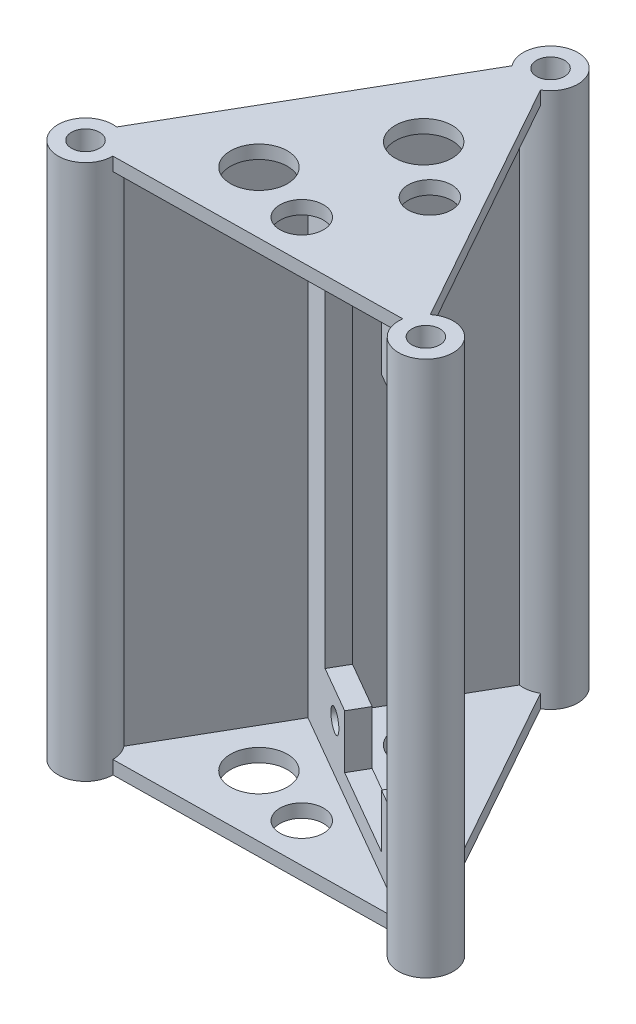
SolidWorks part; units mm, degrees
ref_plane "Front Plane" through (0, 0, 0) normal (0, 0, 1) x (1, 0, 0)
ref_plane "Top Plane" through (0, 0, 0) normal (0, 1, 0) x (1, 0, 0)
ref_plane "Right Plane" through (0, 0, 0) normal (1, 0, 0) x (0, 0, -1)
sketch "Sketch1" plane through (0, 0, 0) normal (0, 1, 0) x (1, 0, 0)
  line L0 (0, 0) -> (0, 38.1)
  circle A0 centre (0, 0) radius 38.1
  circle A1 centre (0, 29.337) radius 1.5875
  circle A2 centre (25.4066, -14.6685) radius 1.5875
  circle A3 centre (-25.4066, -14.6685) radius 1.5875
  point P13 (0, 0)
  dimension "D1" = 76.2
  dimension "D2" = 3.175
  dimension ".345" = 8.763
  dimension "D4" = 3
extrude "Boss-Extrude1" add sketch "Sketch1" along normal blind 10
sketch "Sketch2" plane through (0, 10, 0) normal (0, 1, 0) x (1, 0, 0)
  line L0 (-25.4066, -14.6685) -> (0, 29.337)
  line L1 (-12.7033, 7.3342) -> (25.4066, -14.6685)
  line L2 (-24.1075, -15.4185) -> (1.299, 28.587)
  line L3 (-13.4533, 6.0352) -> (24.6566, -15.9675)
  line L4 (-26.7056, -13.9185) -> (-1.299, 30.087)
  line L5 (-11.9533, 8.6333) -> (26.1566, -13.3695)
  circle A0 centre (-25.4066, -14.6685) radius 1.5875
  circle A1 centre (0, 29.337) radius 1.5875
  circle A2 centre (25.4066, -14.6685) radius 1.5875
  circle A3 centre (-25.4066, -14.6685) radius 2.0875
  circle A4 centre (25.4066, -14.6685) radius 2.0875
  circle A5 centre (0, 29.337) radius 2.0875
  circle A6 centre (-25.4066, -14.6685) radius 4.0875
  circle A7 centre (0, 29.337) radius 4.0875
  circle A8 centre (25.4066, -14.6685) radius 4.0875
  dimension "D1" = 1.5
  dimension "D2" = 1.5
  dimension "D3" = 0.5
  dimension "D4" = 2
extrude "Boss-Extrude2" add sketch "Sketch2" along normal blind 80 separate body contours A7 L4 A6 L0 | A6 L2 L3 L0 | L4 A6 L2 A3 | L0 A6 L4 A3 | L2 A6 L0 A3 | L2 A7 L4 A5 | L4 A7 L0 A5 | L0 A7 L2 A5 | A7 L0 L5 L2 | L0 L3 L2 L1 | L5 L0 L1 L2 | A8 L5 L2 L1 | A8 L1 L2 L3 | L5 A8 L1 A4 | L1 A8 L3 A4 | L3 A8 L5 A4
delete or keep bodies "Body-Delete/Keep 1" type delete bodies bodies 101
sketch "Sketch3" plane through (0, 90, 0) normal (0, 1, 0) x (1, 0, 0)
  line L0 (21.3637, -14.0664) -> (-21.3191, -14.6685)
  line L1 (-12.1543, 5.2852) -> (21.3637, -14.0664) construction
  arc A0 (-24.8045, -10.6256) -> (-22.2064, -12.1256) centre (-25.4066, -14.6685) ccw construction
rib "Rib1" sketch "Sketch3" sketch "Sketch3" thickness 2 extrusion direction parallel to sketch draft on no parameters "D1"=2
sketch "Sketch5" plane through (0, 88, 0) normal (0, -1, 0) x (1, 0, 0)
  line L0 (-22.2064, 12.1256) -> (-12.1543, -5.2852) construction
  line L1 (-12.1543, -5.2852) -> (21.3637, 14.0664) construction
  circle A0 centre (-8.9761, 5.21) radius 4.25
  circle A1 centre (0.6842, 8.4779) radius 3.25
  dimension "D2" = 8.5
  dimension "D6" = 6.5
  dimension "D1" = 8
  dimension "D3" = 7.5
  dimension "D4" = 5.5
  dimension "D5" = 18
extrude "Cut-Extrude1" cut sketch "Sketch5" against normal up to surface (2 mm away) contours A1 | A0 up to face at (25.4066, 90, 16.756)
ref_plane "Plane1" through (0, 0, 0) normal (0.5, 0, -0.866) x (-0.866, 0, -0.5)
ref_plane "Plane2" through (0, 50, 0) normal (0, 1, 0) x (1, 0, 0)
mirror "Mirror1" about plane through (0, 50, 0) normal (0, 1, 0) of "Cut-Extrude1", "Rib1"
mirror "Mirror2" about plane through (0, 0, 0) normal (0.5, 0, -0.866) of "Mirror1", "Rib1", "Cut-Extrude1"
ref_plane "Plane3" through (0, 50, 0) normal (0, -1, 0) x (-1, 0, 0)
ref_plane "Plane4" through (22.8637, 12, 11.4683) normal (0, -1, 0) x (-1, 0, 0)
sketch "Sketch11" plane through (0.75, 0, -1.299) normal (0.5, 0, -0.866) x (-0.866, 0, -0.5)
  line L0 (8.8169, 84.125) -> (13.1685, 84.125) construction
  line L1 (8.8169, 84.125) -> (-21.1831, 84.125)
  line L2 (8.8169, 84.125) -> (8.8169, 15.875)
  line L3 (8.8169, 15.875) -> (-21.1831, 15.875)
  line L4 (-21.1831, 84.125) -> (-21.1831, 15.875)
  line L6 (13.1685, 88) -> (13.1685, 12) construction
  line L7 (8.8169, 84.125) -> (8.8169, 88) construction
  line L8 (13.1685, 88) -> (-25.5347, 88) construction
  line L9 (-21.1831, 84.125) -> (-25.5347, 84.125) construction
  line L10 (-25.5347, 88) -> (-25.5347, 12) construction
  line L11 (8.8169, 15.875) -> (8.8169, 12) construction
  line L12 (-25.5347, 12) -> (13.1685, 12) construction
  dimension "D1" = 68.25
  dimension "D2" = 30
sketch "Sketch12" plane through (-0.75, 0, 1.299) normal (-0.5, 0, 0.866) x (0.866, 0, 0.5)
  line L1 (-2.1971, 80.875) -> (20.8029, 80.875) construction
  line L2 (-2.1971, 80.875) -> (-2.1971, 19.125) construction
  line L3 (-2.1971, 19.125) -> (20.8029, 19.125) construction
  line L4 (20.8029, 80.875) -> (20.8029, 19.125) construction
  line L5 (25.5347, 88) -> (-11.1286, 88) construction
  circle A4 centre (-2.1971, 80.875) radius 1.625
  circle A5 centre (-2.1971, 19.125) radius 1.625
  circle A6 centre (20.8029, 19.125) radius 1.625
  circle A7 centre (20.8029, 80.875) radius 1.625
  dimension "D3" = 3.25
  dimension "D1" = 23
  dimension "D2" = 61.75
  dimension "D4" = 7.125
extrude "Cut-Extrude3" cut sketch "Sketch12" against normal up to surface (3 mm away) up to face at (6.1047, 50, 1.7925)
sketch "Sketch13" plane through (0.75, 0, -1.299) normal (0.5, 0, -0.866) x (-0.866, 0, -0.5)
  line L0 (6.1971, 76.875) -> (6.1971, 23.125)
  line L1 (6.1971, 23.125) -> (-1.8029, 23.125)
  line L2 (-1.8029, 23.125) -> (-1.8029, 15.125)
  line L3 (-1.8029, 15.125) -> (-16.8029, 15.125)
  line L4 (-16.8029, 15.125) -> (-16.8029, 23.125)
  line L5 (-16.8029, 23.125) -> (-24.8029, 23.125)
  line L6 (-24.8029, 23.125) -> (-24.8029, 76.875)
  line L7 (-24.8029, 76.875) -> (-16.8029, 76.875)
  line L8 (-16.8029, 76.875) -> (-16.8029, 84.875)
  line L12 (6.1971, 76.875) -> (-1.8029, 76.875)
  line L13 (-1.8029, 76.875) -> (-1.8029, 84.875)
  line L14 (-1.8029, 84.875) -> (-16.8029, 84.875)
  circle A1 centre (2.1971, 80.875) radius 1.625 construction
  circle A2 centre (-20.8029, 80.875) radius 1.625 construction
  circle A3 centre (2.1971, 19.125) radius 1.625 construction
  dimension "D1" = 4
  dimension "D6" = 4
  dimension "D2" = 4
  dimension "D3" = 4
  dimension "D4" = 4
  dimension "D5" = 4
extrude "Cut-Extrude4" cut sketch "Sketch13" against normal up to surface (3 mm away) up to face at (18.6732, 19.125, 12.513)
